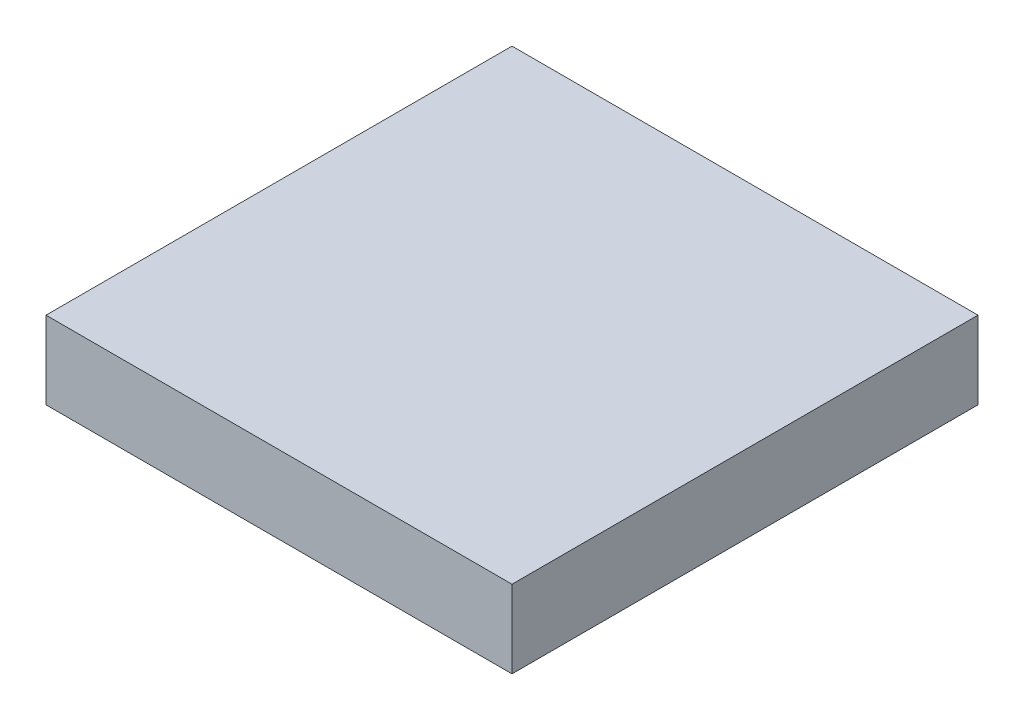
SolidWorks part; units mm, degrees
ref_plane "Front Plane" through (0, 0, 0) normal (0, 0, 1) x (1, 0, 0)
ref_plane "Top Plane" through (0, 0, 0) normal (0, 1, 0) x (1, 0, 0)
ref_plane "Right Plane" through (0, 0, 0) normal (1, 0, 0) x (0, 0, -1)
sketch "Sketch5" plane through (0, 0, 0) normal (0, 1, 0) x (1, 0, 0)
  line L1 (-30, 30) -> (30, 30)
  line L2 (-30, 30) -> (-30, -30)
  line L3 (-30, -30) -> (30, -30)
  line L4 (30, 30) -> (30, -30)
  line L5 (-30, 30) -> (30, -30) construction
  line L6 (-30, -30) -> (30, 30) construction
  point P0 (0, 0)
  dimension "D1" = 60
  dimension "D2" = 60
extrude "Boss-Extrude2" add sketch "Sketch5" along normal blind 10
